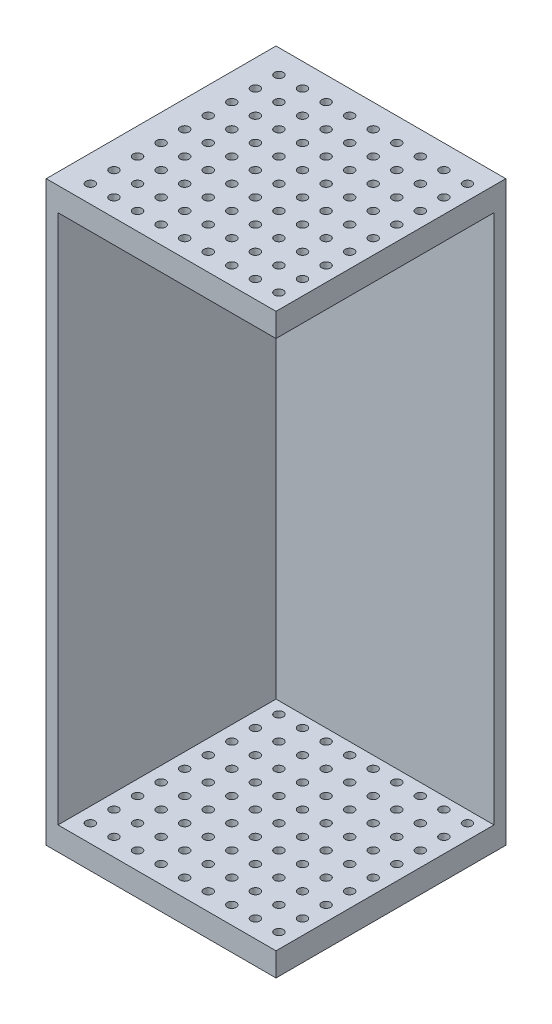
SolidWorks part; units mm, degrees
ref_plane "Front Plane" through (0, 0, 0) normal (0, 0, 1) x (1, 0, 0)
ref_plane "Top Plane" through (0, 0, 0) normal (0, 1, 0) x (1, 0, 0)
ref_plane "Right Plane" through (0, 0, 0) normal (1, 0, 0) x (0, 0, -1)
sketch "Sketch1" plane through (0, 0, 0) normal (0, 1, 0) x (1, 0, 0)
  line L1 (9.75, -9.75) -> (-9.75, -9.75)
  line L2 (9.75, -9.75) -> (9.75, 9.75)
  line L3 (9.75, 9.75) -> (-9.75, 9.75)
  line L4 (-9.75, -9.75) -> (-9.75, 9.75)
  line L5 (9.75, -9.75) -> (-9.75, 9.75) construction
  line L6 (9.75, 9.75) -> (-9.75, -9.75) construction
  point P0 (0, 0)
  dimension "D2" = 19.5
extrude "Boss-Extrude1" add sketch "Sketch1" along normal blind 2
sketch "Sketch2" plane through (0, 2, 0) normal (0, 1, 0) x (1, 0, 0)
  line L0 (-9.75, 9.75) -> (9.75, -9.75) construction
  line L1 (9.75, 9.75) -> (-9.75, -9.75) construction
  line L6 (9.75, -9.75) -> (9.75, 9.75) construction
  line L7 (9.75, 8.75) -> (-8.75, 8.75)
  line L8 (-8.75, 8.75) -> (-8.75, -9.75)
  line L9 (-9.75, -9.75) -> (9.75, -9.75) construction
  line L10 (-8.75, -9.75) -> (-9.75, -9.75)
  line L11 (-9.75, -9.75) -> (-9.75, 9.75)
  line L12 (-9.75, 9.75) -> (9.75, 9.75)
  line L13 (9.75, 9.75) -> (9.75, 8.75)
  dimension "D1" = 1
extrude "Boss-Extrude2" add sketch "Sketch2" along normal blind 45
sketch "Sketch3" plane through (0, 0, 0) normal (0, -1, 0) x (1, 0, 0)
  line L0 (-7.5, 8.25) -> (-7.5, 9.75) construction
  line L1 (9.75, 9.75) -> (-9.75, -9.75) construction
  line L7 (-9.75, 9.75) -> (9.75, 9.75) construction
  line L8 (-9.75, -9.75) -> (-9.75, 9.75) construction
  circle A0 centre (-7.5, 8.25) radius 0.375
  circle A1 centre (-5.5, 8.25) radius 0.375
  circle A2 centre (-3.5, 8.25) radius 0.375
  circle A3 centre (-1.5, 8.25) radius 0.375
  circle A4 centre (0.5, 8.25) radius 0.375
  circle A5 centre (2.5, 8.25) radius 0.375
  circle A6 centre (4.5, 8.25) radius 0.375
  circle A7 centre (6.5, 8.25) radius 0.375
  circle A8 centre (8.5, 8.25) radius 0.375
  circle A9 centre (-5.5, 6.25) radius 0.375
  circle A10 centre (-3.5, 6.25) radius 0.375
  circle A11 centre (-1.5, 6.25) radius 0.375
  circle A12 centre (0.5, 6.25) radius 0.375
  circle A13 centre (2.5, 6.25) radius 0.375
  circle A14 centre (4.5, 6.25) radius 0.375
  circle A15 centre (6.5, 6.25) radius 0.375
  circle A16 centre (8.5, 6.25) radius 0.375
  circle A17 centre (-5.5, 4.25) radius 0.375
  circle A18 centre (-3.5, 4.25) radius 0.375
  circle A19 centre (-1.5, 4.25) radius 0.375
  circle A20 centre (0.5, 4.25) radius 0.375
  circle A21 centre (2.5, 4.25) radius 0.375
  circle A22 centre (4.5, 4.25) radius 0.375
  circle A23 centre (6.5, 4.25) radius 0.375
  circle A24 centre (8.5, 4.25) radius 0.375
  circle A25 centre (-5.5, 2.25) radius 0.375
  circle A26 centre (-3.5, 2.25) radius 0.375
  circle A27 centre (-1.5, 2.25) radius 0.375
  circle A28 centre (0.5, 2.25) radius 0.375
  circle A29 centre (2.5, 2.25) radius 0.375
  circle A30 centre (4.5, 2.25) radius 0.375
  circle A31 centre (6.5, 2.25) radius 0.375
  circle A32 centre (8.5, 2.25) radius 0.375
  circle A33 centre (-5.5, 0.25) radius 0.375
  circle A34 centre (-3.5, 0.25) radius 0.375
  circle A35 centre (-1.5, 0.25) radius 0.375
  circle A36 centre (0.5, 0.25) radius 0.375
  circle A37 centre (2.5, 0.25) radius 0.375
  circle A38 centre (4.5, 0.25) radius 0.375
  circle A39 centre (6.5, 0.25) radius 0.375
  circle A40 centre (8.5, 0.25) radius 0.375
  circle A41 centre (-5.5, -1.75) radius 0.375
  circle A42 centre (-3.5, -1.75) radius 0.375
  circle A43 centre (-1.5, -1.75) radius 0.375
  circle A44 centre (0.5, -1.75) radius 0.375
  circle A45 centre (2.5, -1.75) radius 0.375
  circle A46 centre (4.5, -1.75) radius 0.375
  circle A47 centre (6.5, -1.75) radius 0.375
  circle A48 centre (8.5, -1.75) radius 0.375
  circle A49 centre (-5.5, -3.75) radius 0.375
  circle A50 centre (-3.5, -3.75) radius 0.375
  circle A51 centre (-1.5, -3.75) radius 0.375
  circle A52 centre (0.5, -3.75) radius 0.375
  circle A53 centre (2.5, -3.75) radius 0.375
  circle A54 centre (4.5, -3.75) radius 0.375
  circle A55 centre (6.5, -3.75) radius 0.375
  circle A56 centre (8.5, -3.75) radius 0.375
  circle A57 centre (-5.5, -5.75) radius 0.375
  circle A58 centre (-3.5, -5.75) radius 0.375
  circle A59 centre (-1.5, -5.75) radius 0.375
  circle A60 centre (0.5, -5.75) radius 0.375
  circle A61 centre (2.5, -5.75) radius 0.375
  circle A62 centre (4.5, -5.75) radius 0.375
  circle A63 centre (6.5, -5.75) radius 0.375
  circle A64 centre (8.5, -5.75) radius 0.375
  circle A65 centre (-5.5, -7.75) radius 0.375
  circle A66 centre (-3.5, -7.75) radius 0.375
  circle A67 centre (-1.5, -7.75) radius 0.375
  circle A68 centre (0.5, -7.75) radius 0.375
  circle A69 centre (2.5, -7.75) radius 0.375
  circle A70 centre (4.5, -7.75) radius 0.375
  circle A71 centre (6.5, -7.75) radius 0.375
  circle A72 centre (8.5, -7.75) radius 0.375
  circle A73 centre (-7.5, 6.25) radius 0.375
  circle A74 centre (-7.5, 4.25) radius 0.375
  circle A75 centre (-7.5, 2.25) radius 0.375
  circle A76 centre (-7.5, 0.25) radius 0.375
  circle A77 centre (-7.5, -1.75) radius 0.375
  circle A78 centre (-7.5, -3.75) radius 0.375
  circle A79 centre (-7.5, -5.75) radius 0.375
  circle A80 centre (-7.5, -7.75) radius 0.375
  dimension "D1" = 0.75
  dimension "D2" = 9
  dimension "D4" = 1.5
  dimension "D5" = 2.25
sketch "Sketch5" plane through (0, 47, 0) normal (0, 1, 0) x (1, 0, 0)
  line L1 (9.75, -9.75) -> (-9.75, -9.75)
  line L2 (9.75, -9.75) -> (9.75, 9.75)
  line L3 (9.75, 9.75) -> (-9.75, 9.75)
  line L4 (-9.75, -9.75) -> (-9.75, 9.75)
  line L5 (9.75, -9.75) -> (-9.75, 9.75) construction
  line L6 (9.75, 9.75) -> (-9.75, -9.75) construction
  point P0 (0, 0)
extrude "Boss-Extrude5" add sketch "Sketch5" along normal blind 2
extrude "Cut-Extrude1" cut sketch "Sketch3" against normal through all
